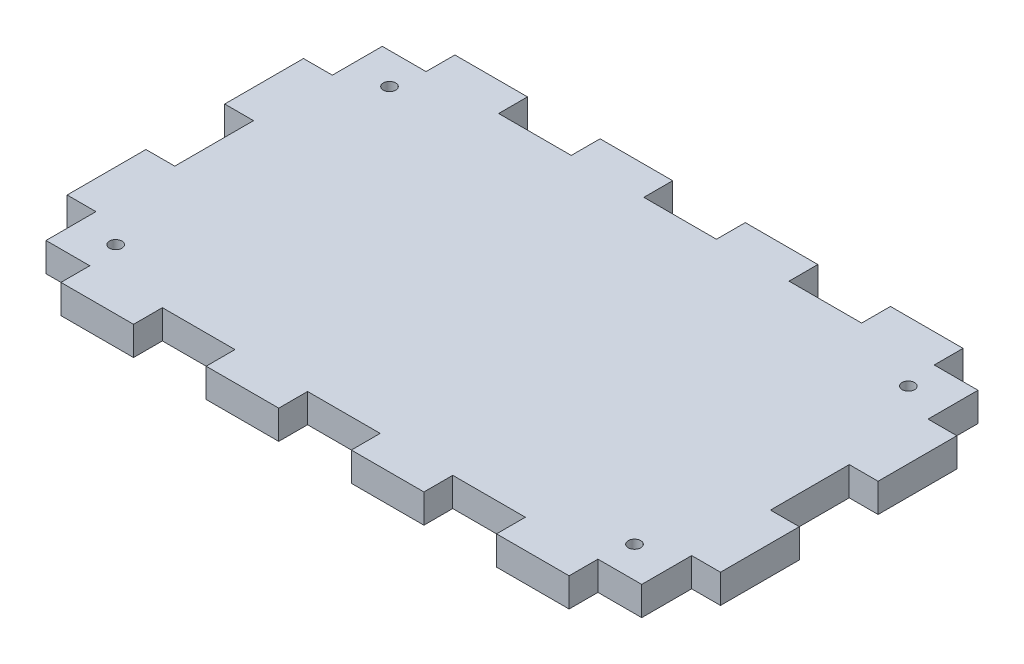
SolidWorks part; units mm, degrees
ref_plane "Front" through (0, 0, 0) normal (0, 0, 1) x (1, 0, 0)
ref_plane "Top" through (0, 0, 0) normal (0, 1, 0) x (1, 0, 0)
ref_plane "Right" through (0, 0, 0) normal (1, 0, 0) x (0, 0, -1)
sketch "Skizze1" plane through (0, 0, 0) normal (0, 1, 0) x (1, 0, 0)
  line L1 (0, 0) -> (68, 0) construction
  line L2 (0, 0) -> (0, 41) construction
  line L3 (0, 41) -> (68, 41) construction
  line L4 (68, 0) -> (68, 41) construction
  line L88 (3, 37.9994) -> (3, 32.8)
  line L89 (3, 32.8) -> (0, 32.8)
  line L90 (0, 32.8) -> (0, 24.5991)
  line L91 (3, 24.5991) -> (0, 24.5991)
  line L92 (3, 24.5991) -> (3, 16.3998)
  line L93 (3, 16.3998) -> (0, 16.3998)
  line L94 (0, 16.3998) -> (0, 8.1991)
  line L95 (3, 8.1991) -> (0, 8.1991)
  line L96 (3, 8.1991) -> (3, 3)
  line L97 (65.0006, 37.9994) -> (65.0006, 32.8)
  line L98 (68.0009, 32.8) -> (65.0006, 32.8)
  line L99 (68.0009, 32.8) -> (68.0009, 24.5991)
  line L100 (68.0009, 24.5991) -> (65.0006, 24.5991)
  line L101 (65.0006, 24.5991) -> (65.0006, 16.3998)
  line L102 (68.0009, 16.3998) -> (65.0006, 16.3998)
  line L103 (68.0009, 16.3998) -> (68.0009, 8.1991)
  line L104 (68.0009, 8.1991) -> (65.0006, 8.1991)
  line L105 (65.0006, 8.1991) -> (65.0006, 3)
  line L106 (3, 37.9994) -> (7.5557, 37.9994)
  line L107 (7.5557, 37.9994) -> (7.5557, 40.9994)
  line L108 (7.5557, 40.9994) -> (15.1117, 40.9994)
  line L109 (15.1117, 37.9994) -> (15.1117, 40.9994)
  line L110 (15.1117, 37.9994) -> (22.6675, 37.9994)
  line L111 (22.6675, 37.9994) -> (22.6675, 40.9994)
  line L112 (22.6675, 40.9994) -> (30.2232, 40.9994)
  line L113 (30.2232, 37.9994) -> (30.2232, 40.9994)
  line L114 (30.2232, 37.9994) -> (37.7789, 37.9994)
  line L115 (37.7789, 37.9994) -> (37.7789, 40.9994)
  line L116 (37.7789, 40.9994) -> (45.3334, 40.9994)
  line L117 (45.3334, 37.9994) -> (45.3334, 40.9994)
  line L118 (45.3334, 37.9994) -> (52.8892, 37.9994)
  line L119 (52.8892, 37.9994) -> (52.8892, 40.9994)
  line L120 (52.8892, 40.9994) -> (60.4449, 40.9994)
  line L121 (60.4449, 37.9994) -> (60.4449, 40.9994)
  line L122 (60.4449, 37.9994) -> (65.0006, 37.9994)
  line L123 (3, 3) -> (7.5557, 3)
  line L124 (7.5557, 0) -> (7.5557, 3)
  line L125 (7.5557, 0) -> (15.1117, 0)
  line L126 (15.1117, 0) -> (15.1117, 3)
  line L127 (15.1117, 3) -> (22.6675, 3)
  line L128 (22.6675, 0) -> (22.6675, 3)
  line L129 (22.6675, 0) -> (30.2232, 0)
  line L130 (30.2232, 0) -> (30.2232, 3)
  line L131 (30.2232, 3) -> (37.7789, 3)
  line L132 (37.7789, 0) -> (37.7789, 3)
  line L133 (37.7789, 0) -> (45.3334, 0)
  line L134 (45.3334, 0) -> (45.3334, 3)
  line L135 (45.3334, 3) -> (52.8891, 3)
  line L136 (52.8891, 0) -> (52.8891, 3)
  line L137 (52.8891, 0) -> (60.4449, 0)
  line L138 (60.4449, 0) -> (60.4449, 3)
  line L139 (60.4449, 3) -> (65.0006, 3)
  dimension "D1" = 68
  dimension "D2" = 41
extrude "Aufsatz-Linear austragen1" add sketch "Skizze1" along normal blind 3
sketch "Skizze2" plane through (0, 3, 0) normal (0, 1, 0) x (1, 0, 0)
  line L0 (3, 20.4995) -> (7.0011, 20.4995) construction
  line L1 (7.0011, 34.7495) -> (61.0011, 34.7495) construction
  line L2 (7.0011, 34.7495) -> (7.0011, 6.2495) construction
  line L3 (7.0011, 6.2495) -> (61.0011, 6.2495) construction
  line L4 (61.0011, 34.7495) -> (61.0011, 6.2495) construction
  line L5 (3, 24.5991) -> (3, 16.3998) construction
  line L6 (34.0011, 37.9994) -> (34.0011, 34.7495) construction
  line L7 (37.7789, 37.9994) -> (30.2232, 37.9994) construction
  circle A0 centre (7.0011, 34.7495) radius 0.65
  circle A1 centre (61.0011, 34.7495) radius 0.65
  circle A2 centre (61.0011, 6.2495) radius 0.65
  circle A3 centre (7.0011, 6.2495) radius 0.65
  dimension "D1" = 1.3
  dimension "D2" = 28.5
  dimension "D3" = 54
extrude "Schnitt-Linear austragen1" cut sketch "Skizze2" against normal up to next
sketch "Skizze3" [suppressed] plane through (0, 3, 0) normal (0, 1, 0) x (1, 0, 0)
  line L0 (65.0006, 32.8) -> (65.0006, 37.9994) construction
  line L1 (37.7789, 37.9994) -> (30.2232, 37.9994) construction
  line L2 (65.0006, 3) -> (65.0006, 8.1991) construction
  line L5 (45.3334, 3) -> (52.8891, 3) construction
  circle A0 centre (26.0006, 35.9994) radius 1.75
  circle A1 centre (52.5006, 7) radius 2.1
  circle A2 centre (16.0006, 7) radius 2.1
  dimension "D1" = 39
  dimension "D2" = 3.5
  dimension "D4" = 4.2
  dimension "D3" = 2
  dimension "D5" = 12.5
  dimension "D6" = 4
  dimension "D7" = 36.5
extrude "Schnitt-Linear austragen2" [suppressed] cut sketch "Skizze3" against normal up to next
equation "\"D4@Skizze4\"=\"D1@Skizze4\""
